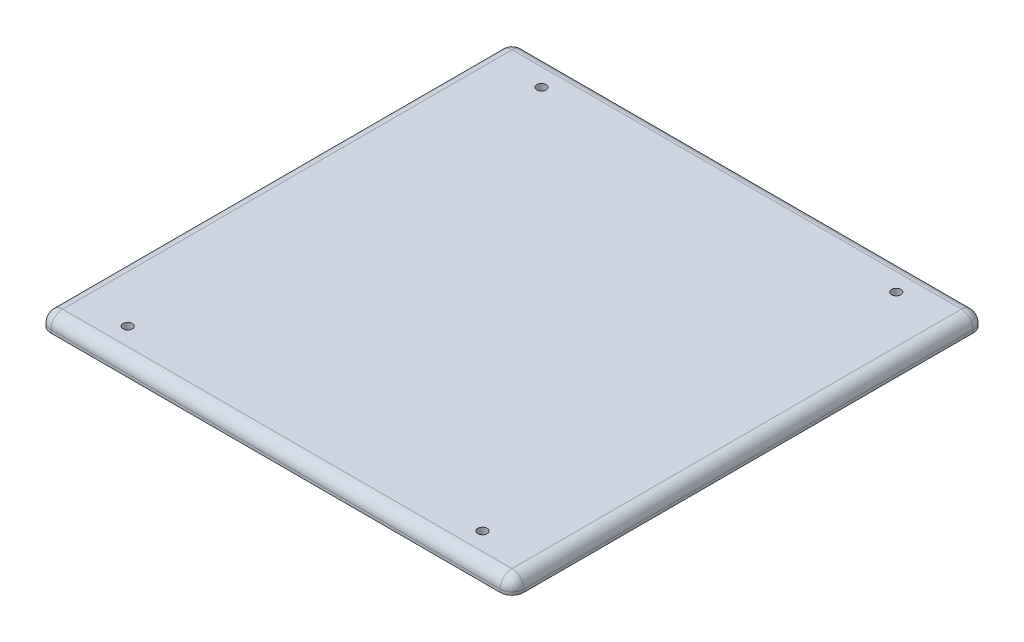
SolidWorks part; units mm, degrees
ref_plane "Front Plane" through (0, 0, 0) normal (0, 0, 1) x (1, 0, 0)
ref_plane "Top Plane" through (0, 0, 0) normal (0, 1, 0) x (1, 0, 0)
ref_plane "Right Plane" through (0, 0, 0) normal (1, 0, 0) x (0, 0, -1)
sketch "Sketch1" plane through (0, 0, 0) normal (0, 1, 0) x (1, 0, 0)
  line L1 (50.8, -50.8) -> (-50.8, -50.8)
  line L2 (50.8, -50.8) -> (50.8, 50.8)
  line L3 (50.8, 50.8) -> (-50.8, 50.8)
  line L4 (-50.8, -50.8) -> (-50.8, 50.8)
  line L5 (50.8, -50.8) -> (-50.8, 50.8) construction
  line L6 (50.8, 50.8) -> (-50.8, -50.8) construction
  point P0 (0, 0)
  dimension "D1" = 101.6
  dimension "D2" = 101.6
extrude "Boss-Extrude1" add sketch "Sketch1" along normal blind 3.175
sketch "Sketch2" plane through (0, 3.175, 0) normal (0, 1, 0) x (1, 0, 0)
  line L0 (0, 0) -> (0, -50.8) construction
  line L1 (-50.8, -50.8) -> (50.8, -50.8) construction
  line L2 (0, 0) -> (50.8, 0) construction
  line L3 (50.8, -50.8) -> (50.8, 50.8) construction
  line L4 (-50.8, 50.8) -> (-50.8, -50.8) construction
  circle A0 centre (-38.1, -44.45) radius 0.9995
  circle A1 centre (38.1, -44.45) radius 0.9995
  circle A2 centre (38.1, 44.45) radius 0.9995
  circle A3 centre (-38.1, 44.45) radius 0.9995
  dimension "D3" = 1.999
  dimension "D1" = 12.7
  dimension "D2" = 6.35
extrude "Cut-Extrude1" cut sketch "Sketch2" against normal blind 3.175
chamfer "Chamfer1" distance 1.27 angle 45 4 edges at (-38.1, 0, 45.4495) (38.1, 0, 43.4505) (-38.1, 0, -45.4495) (38.1, 0, -43.4505)
fillet "Fillet1" radius 2.54 8 edges at (-50.8, 1.5875, 50.8) (-50.8, 1.5875, -50.8) (50.8, 1.5875, -50.8) (50.8, 1.5875, 50.8) (0, 3.175, 50.8) (50.8, 3.175, 0) (0, 3.175, -50.8) (-50.8, 3.175, 0)
